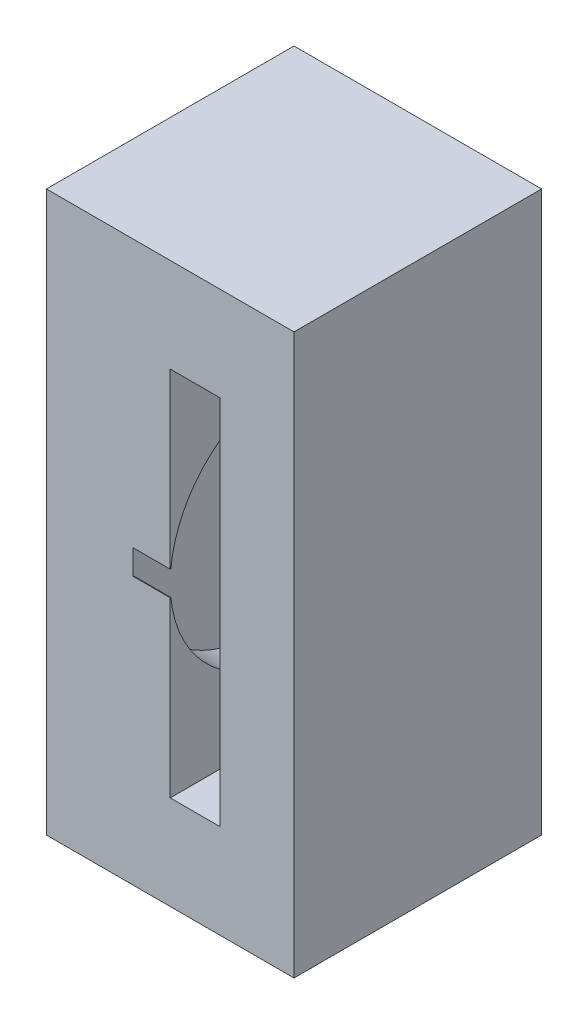
SolidWorks part; units mm, degrees
other "Markup1"
sketch "Sketch4" plane through (-50, 0, 50.1) normal (-0.123, -0.9831, 0.136) x (-0.0115, 0.1384, 0.9903)
ref_plane "Alzado" through (0, 0, 0) normal (0, 0, 1) x (1, 0, 0)
ref_plane "Planta" through (0, 0, 0) normal (0, 1, 0) x (1, 0, 0)
ref_plane "Vista lateral" through (0, 0, 0) normal (1, 0, 0) x (0, 0, -1)
sketch "Sketch1" plane through (0, 0, 0) normal (0, 1, 0) x (1, 0, 0)
  line L1 (-50, 50) -> (50, 50)
  line L2 (-50, 50) -> (-50, -50)
  line L3 (-50, -50) -> (50, -50)
  line L4 (50, 50) -> (50, -50)
  line L5 (-50, 50) -> (50, -50) construction
  line L6 (-50, -50) -> (50, 50) construction
  point P0 (0, 0)
  dimension "D1" = 100
  dimension "D2" = 100
extrude "Boss-Extrude1" add sketch "Sketch1" along normal blind 226
sketch "Sketch2" plane through (0, 0, 50) normal (0, 0, 1) x (1, 0, 0)
  line L0 (-50, 226) -> (-50, 0) construction
  circle A0 centre (0, 113) radius 5
  point P4 (-50, 113)
  dimension "D1" = 10
sketch "Sketch5" plane through (0, 0, -50) normal (0, 0, -1) x (-1, 0, 0)
  line L0 (0, 226) -> (0, 0) construction
  line L5 (-50, 226) -> (50, 226) construction
  line L6 (-20.1, 188) -> (-20.1, 38)
  line L7 (-20.1, 38) -> (15, 38)
  line L8 (15, 38) -> (15, 188)
  line L9 (15, 188) -> (-20.1, 188)
  line L11 (-20.1, 38) -> (-20, 38)
  line L12 (-20.1, 38) -> (-20.1, 93)
  line L15 (-20.1, 188) -> (-20, 188)
  line L16 (-20.1, 188) -> (-20.1, 133)
  point P9 (15, 113)
  dimension "D1" = 20.1
  dimension "D2" = 15
  dimension "D3" = 150
extrude "Cut-Extrude1" cut sketch "Sketch5" against normal through all
sketch "Sketch6" plane through (-15, 0, 0) normal (1, 0, 0) x (0, 0, -1)
  line L0 (-50, 113) -> (0, 113) construction
  line L1 (0, 116.2887) -> (0, 106.75) construction
  line L2 (-2, 118.9214) -> (-2, 107.0786)
  line L5 (-50, 38) -> (50, 38)
  line L6 (50, 38) -> (50, 188)
  line L7 (50, 188) -> (-50, 188)
  line L9 (-50, 38) -> (50, 38)
  line L10 (50, 38) -> (50, 108)
  line L11 (50, 188) -> (-50, 188)
  line L12 (2, 118.9214) -> (2, 107.0786)
  line L13 (-50, 113) -> (50, 113) construction
  line L14 (-50, 108) -> (50, 108)
  line L15 (-50, 118) -> (50, 118)
  line L16 (-50, 108) -> (-50, 38)
  line L17 (-50, 188) -> (-50, 38)
  line L18 (-50, 188) -> (-50, 118)
  line L19 (50, 118) -> (50, 188)
  arc A0 (-2, 118.9214) -> (-2, 107.0786) centre (0, 113) ccw
  arc A1 (-49.7494, 108) -> (49.7494, 108) centre (0, 113) ccw
  arc A3 (49.7494, 118) -> (-49.7494, 118) centre (0, 113) ccw
  arc A5 (2, 118.9214) -> (2, 107.0786) centre (0, 113) cw
  line M9 (-50, 38) -> (50, 38)
  line M10 (50, 38) -> (50, 188)
  line M11 (50, 188) -> (-50, 188)
  line M24 (-50, 188) -> (-50, 38)
  dimension "D3" = 12.5
  dimension "D4" = 100
  dimension "D2" = 5
  dimension "D5" = 2
  dimension "D6" = 5
  dimension "D1" = 0
extrude "Boss-Extrude2" add sketch "Sketch6" along normal blind 15 contours A1 L14 M24 M9 M10 | A3 L15 M10 M11 M24 | A5 L15 L12 L14 | L15 A0 L14 L2 | A5 L12 L15 | L14 A0 L2
sketch "Sketch8" plane through (0, 0, 50) normal (0, 0, 1) x (1, 0, 0)
  line L0 (17.778, 226) -> (17.778, 0)
  line L1 (-50, 226) -> (50, 226) construction
  line L2 (-50, 0) -> (50, 0) construction
  line L3 (17.778, 0) -> (50, 0)
  line L4 (50, 0) -> (50, 226)
  line L5 (50, 226) -> (17.778, 226)
extrude "Cut-Extrude3" [suppressed] cut sketch "Sketch8" against normal through all
sketch "Sketch9" plane through (0, 0, 0) normal (0, 0, 1) x (1, 0, 0)
  line L0 (17.778, 226) -> (17.778, 0)
  line L6 (-50, 226) -> (-50, 0)
  line L7 (-50, 0) -> (17.778, 0)
  line L8 (17.778, 226) -> (-50, 226)
extrude "Cut-Extrude4" [suppressed] cut sketch "Sketch9" against normal through all both and the other way through all
sketch "Sketch10" plane through (20.1, 0, 0) normal (-1, 0, 0) x (0, 0, 1)
  line L0 (-50, 188) -> (-50, 38) construction
  line L1 (0, 123.5799) -> (0, 101.7698) construction
  line L2 (-2, 119.1847) -> (-2, 106.8153)
  line L3 (2, 119.1847) -> (2, 106.8153)
  arc A0 (-2, 119.1847) -> (-2, 106.8153) centre (0, 113) ccw
  arc A1 (2, 106.8153) -> (2, 119.1847) centre (0, 113) ccw
  point P7 (-50, 113)
  dimension "D1" = 13
  dimension "D2" = 2
extrude "Boss-Extrude4" add sketch "Sketch10" along normal blind 19
fillet "Fillet1" [suppressed] radius 10
